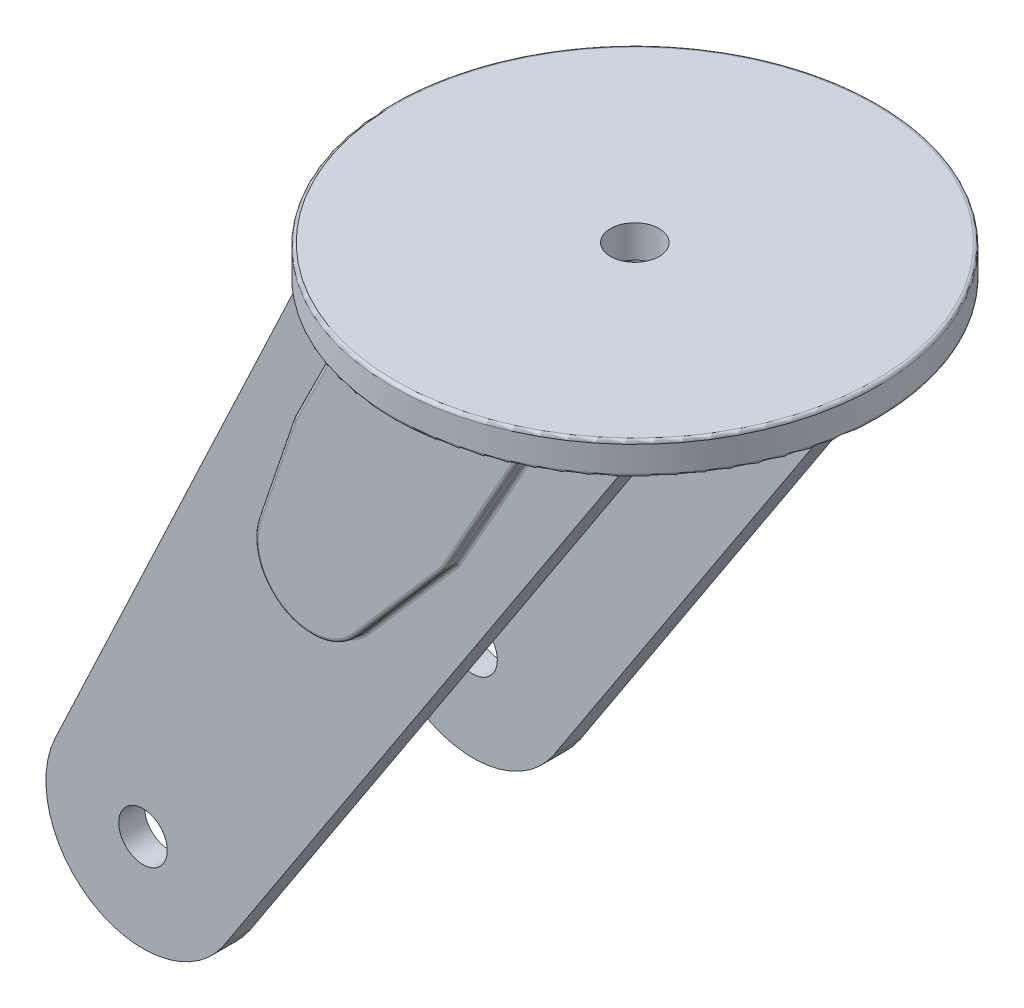
SolidWorks part; units mm, degrees
ref_plane "Front" through (0, 0, 0) normal (0, 0, 1) x (1, 0, 0)
ref_plane "Top" through (0, 0, 0) normal (0, 1, 0) x (1, 0, 0)
ref_plane "Right" through (0, 0, 0) normal (1, 0, 0) x (0, 0, -1)
sketch "Sketch1" plane through (0, 0, 0) normal (0, 1, 0) x (1, 0, 0)
  circle A0 centre (0, 0) radius 75
  dimension "D1" = 150
extrude "Boss-Extrude1" add sketch "Sketch1" along normal blind 10
fillet "Fillet1" radius 1 2 edges at (0, 0, 75) (0, 10, 75)
ref_plane "Plane1" through (0, 0, 47) normal (0, 0, 1) x (1, 0, 0)
sketch "Sketch2" plane through (0, 0, 47) normal (0, 0, 1) x (1, 0, 0)
  line L0 (-50, 0) -> (50, 0)
  line L1 (-74, 0) -> (74, 0) construction
  line L2 (50, 0) -> (-71.8911, -186.4177)
  line L3 (-50, 0) -> (-124.1342, -157.2041)
  arc A0 (-124.1342, -157.2041) -> (-71.8911, -186.4177) centre (-97, -170) ccw
  circle A1 centre (-97, -170) radius 7.5
  point P6 (0, 0)
  dimension "D2" = 60
  dimension "D4" = 147
  dimension "D5" = 15
  dimension "D1" = 100
  dimension "D3" = 170
extrude "Boss-Extrude2" add sketch "Sketch2" along normal blind 8
sketch "Sketch3" plane through (0, 0, 55) normal (0, 0, 1) x (1, 0, 0)
  line L0 (27.2479, 0) -> (0, -48.2764)
  line L1 (49.5076, 0) -> (-49.5076, 0) construction
  line L2 (0, -48.2764) -> (-27.6778, -80.1117)
  line L3 (-31.2904, 0) -> (-46.5614, -30.5789)
  line L4 (-46.5614, -30.5789) -> (-57.5087, -63.0074)
  line L5 (-31.2904, 0) -> (27.2479, 0)
  arc A0 (-57.5087, -63.0074) -> (-27.6778, -80.1117) centre (-40.9038, -68.613) ccw
  point P9 (-44.4072, -31.4673)
  point P10 (0, 0)
  point P11 (-46.5614, -30.5789)
extrude "Boss-Extrude3" add sketch "Sketch3" along normal blind 4
fillet "Fillet2" radius 1 12 edges at (-13.8389, -64.1941, 59) (-49.6212, -83.8167, 59) (-13.8389, -64.1941, 55) (-49.6212, -83.8167, 55) (13.624, -24.1382, 55) (13.624, -24.1382, 59) (-38.9259, -15.2894, 59) (-38.9259, -15.2894, 55) (0, -48.2764, 57) (-52.0351, -46.7931, 55) (-46.5614, -30.5789, 57) (-52.0351, -46.7931, 59)
sketch "Sketch4" plane through (0, 0, 47) normal (0, 0, -1) x (-1, 0, 0)
  line L5 (-27.2479, 0) -> (0, -48.2764)
  line L6 (0, -48.2764) -> (27.6778, -80.1117)
  line L7 (57.5087, -63.0074) -> (46.5614, -30.5789)
  line L8 (46.5614, -30.5789) -> (31.2904, 0)
  line L9 (31.2904, 0) -> (-27.2479, 0)
  line L10 (-27.2479, 0) -> (0, -48.2764)
  line L11 (0, -48.2764) -> (27.6778, -80.1117)
  line L12 (57.5087, -63.0074) -> (46.5614, -30.5789)
  line L13 (46.5614, -30.5789) -> (31.2904, 0)
  line L14 (31.2904, 0) -> (-27.2479, 0)
  arc A1 (27.6778, -80.1117) -> (57.5087, -63.0074) centre (40.9038, -68.613) ccw
  arc A2 (27.6778, -80.1117) -> (57.5087, -63.0074) centre (40.9038, -68.613) ccw
  dimension "D1" = 0
extrude "Cut-Extrude1" cut sketch "Sketch4" against normal blind 4
fillet "Fillet3" radius 1 12 edges at (-38.9259, -15.2894, 47) (-38.9259, -15.2894, 51) (-49.6212, -83.8167, 51) (-52.0351, -46.7931, 51) (-46.5614, -30.5789, 49) (-52.0351, -46.7931, 47) (-49.6212, -83.8167, 47) (-13.8389, -64.1941, 47) (0, -48.2764, 49) (-13.8389, -64.1941, 51) (13.624, -24.1382, 51) (13.624, -24.1382, 47)
mirror "Mirror1" about plane through (0, 0, 0) normal (0, 0, 1) of "Boss-Extrude2", "Boss-Extrude3", "Cut-Extrude1", "Fillet3"
sketch "Sketch5" plane through (0, 10, 0) normal (0, 1, 0) x (1, 0, 0)
  circle A1 centre (0, 0) radius 7.5
  dimension "D1" = 15
extrude "Cut-Extrude2" cut sketch "Sketch5" against normal through all
